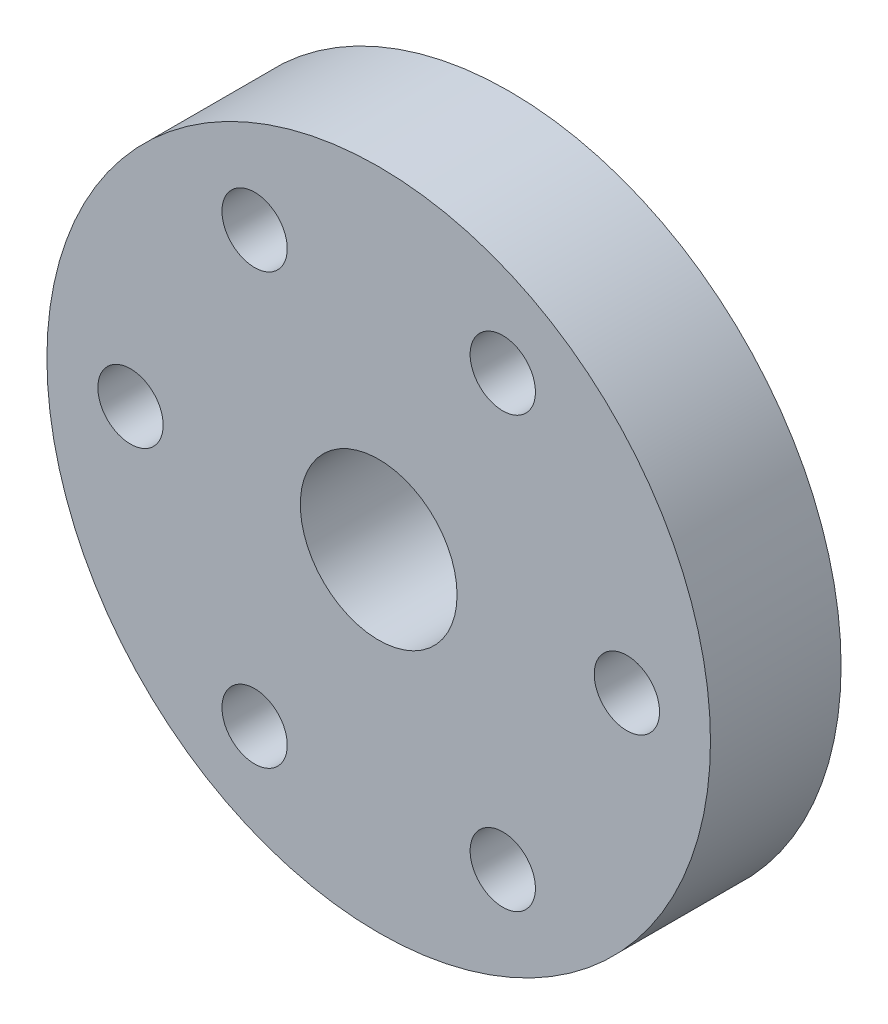
SolidWorks part; units mm, degrees
ref_plane "Front Plane" through (0, 0, 0) normal (0, 0, 1) x (1, 0, 0)
ref_plane "Top Plane" through (0, 0, 0) normal (0, 1, 0) x (1, 0, 0)
ref_plane "Right Plane" through (0, 0, 0) normal (1, 0, 0) x (0, 0, -1)
sketch "Sketch1" plane through (0, 0, 0) normal (1, 0, 0) x (0, 0, -1)
  line L0 (-50.269, 0) -> (56.3994, 0) construction
  line L1 (0, 3) -> (0, 12.7)
  line L2 (0, 12.7) -> (5, 12.7)
  line L3 (5, 12.7) -> (5, 6)
  line L4 (5, 6) -> (9.2, 6)
  line L5 (9.2, 6) -> (9.2, 3)
  line L6 (9.2, 3) -> (0, 3)
  dimension "D1" = 25.4
  dimension "D2" = 5
  dimension "D3" = 12
  dimension "D4" = 3
  dimension "D5" = 4.2
revolve "Revolve1" add sketch "Sketch1" angle 360 about L0
sketch "Sketch2" plane through (0, 0, 0) normal (0, 0, 1) x (1, 0, 0)
  line L0 (0, 0) -> (12.7, 0) construction
  circle A0 centre (0, 0) radius 12.7 construction
  point P6 (9.5, 0)
  point P7 (4.75, -8.2272)
  point P10 (-4.75, -8.2272)
  point P11 (-9.5, 0)
  point P12 (-4.75, 8.2272)
  point P13 (4.75, 8.2272)
  point P14 (0, 0)
  dimension "D1" = 9.5
  dimension "D2" = 6
hole_wizard "Tap Drill for M3x0.5 Tap1" positions "Sketch3" profile "Sketch4" hole size "M3x0.5" standard "ANSI Metric"
sketch "Sketch3" plane through (0, 0, 0) normal (0, 0, 1) x (1, 0, 0)
  point P0 (-4.75, 8.2272)
  point P3 (4.75, 8.2272)
  point P6 (9.5, 0)
  point P9 (4.75, -8.2272)
  point P12 (-4.75, -8.2272)
  point P15 (-9.5, 0)
sketch "Sketch4" plane through (-4.75, 8.2272, 0) normal (1, 0, 0) x (0, -1, 0)
  line L0 (0, 0) -> (0, 10.7511)
  line L1 (0, 10.7511) -> (1.25, 10)
  line L2 (1.25, 10) -> (1.25, 0)
  line L5 (1.25, 0) -> (0, 0)
  line L10 (0, 10.7511) -> (-1.25, 10) construction
  line L11 (0, -6.35) -> (0, 107.95) construction
  dimension "Hole Dia." = 2.5
  dimension "Hole Depth" = 10
  dimension "Drill Angle" = 118
